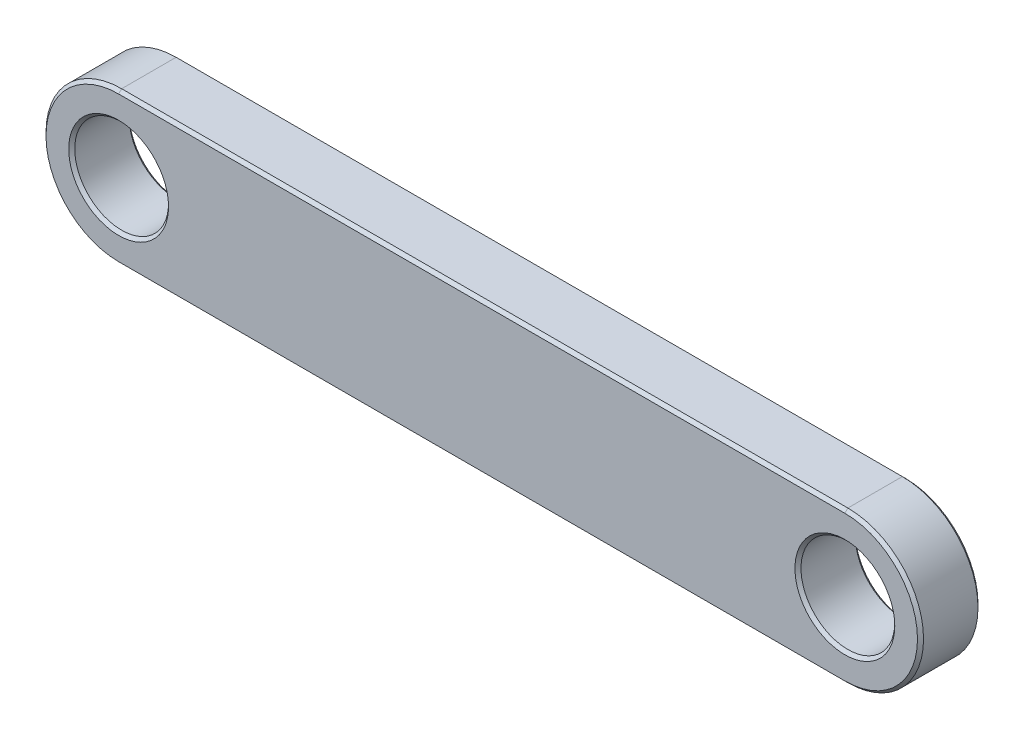
SolidWorks part; units mm, degrees
material "Copper"
ref_plane "Front Plane" through (0, 0, 0) normal (0, 0, 1) x (1, 0, 0)
ref_plane "Top Plane" through (0, 0, 0) normal (0, 1, 0) x (1, 0, 0)
ref_plane "Right Plane" through (0, 0, 0) normal (1, 0, 0) x (0, 0, -1)
sketch "Sketch1" plane through (0, 0, 0) normal (0, 0, 1) x (1, 0, 0)
  line L0 (-12, 0) -> (12, 0) construction
  line L1 (-12, 2.5) -> (12, 2.5)
  line L2 (-12, -2.5) -> (12, -2.5)
  arc A0 (-12, 2.5) -> (-12, -2.5) centre (-12, 0) ccw
  arc A1 (12, -2.5) -> (12, 2.5) centre (12, 0) ccw
  point P2 (0, 0)
  dimension "D2" = 2.5
  dimension "D1" = 24
extrude "Boss-Extrude1" add sketch "Sketch1" along normal blind 2
sketch "Sketch2" plane through (0, 0, 2) normal (0, 0, 1) x (1, 0, 0)
  circle A0 centre (-12, 0) radius 1.55
  circle A1 centre (12, 0) radius 1.55
  dimension "D1" = 3.1
  dimension "D2" = 3.1
extrude "Cut-Extrude1" cut sketch "Sketch2" against normal blind 2
chamfer "Chamfer1" distance 0.1 angle 45 12 edges at (0, -2.5, 2) (14.5, 0, 2) (-14.5, 0, 2) (0, 2.5, 2) (0, 2.5, 0) (-14.5, 0, 0) (14.5, 0, 0) (0, -2.5, 0) (13.55, 0, 0) (13.55, 0, 2) (-10.45, 0, 0) (-10.45, 0, 2)
